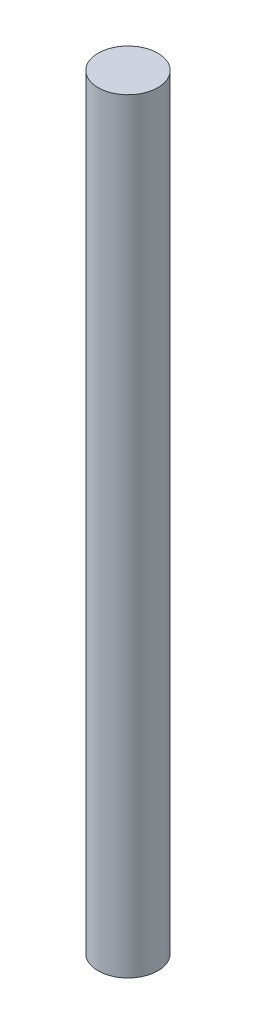
SolidWorks part; units mm, degrees
ref_plane "Front Plane" through (0, 0, 0) normal (0, 0, 1) x (1, 0, 0)
ref_plane "Top Plane" through (0, 0, 0) normal (0, 1, 0) x (1, 0, 0)
ref_plane "Right Plane" through (0, 0, 0) normal (1, 0, 0) x (0, 0, -1)
sketch "Sketch1" plane through (0, 0, 0) normal (0, 1, 0) x (1, 0, 0)
  circle A0 centre (0, 0) radius 3.9688
  dimension "D1" = 7.9375
extrude "Boss-Extrude1" add sketch "Sketch1" along normal blind 101.6
